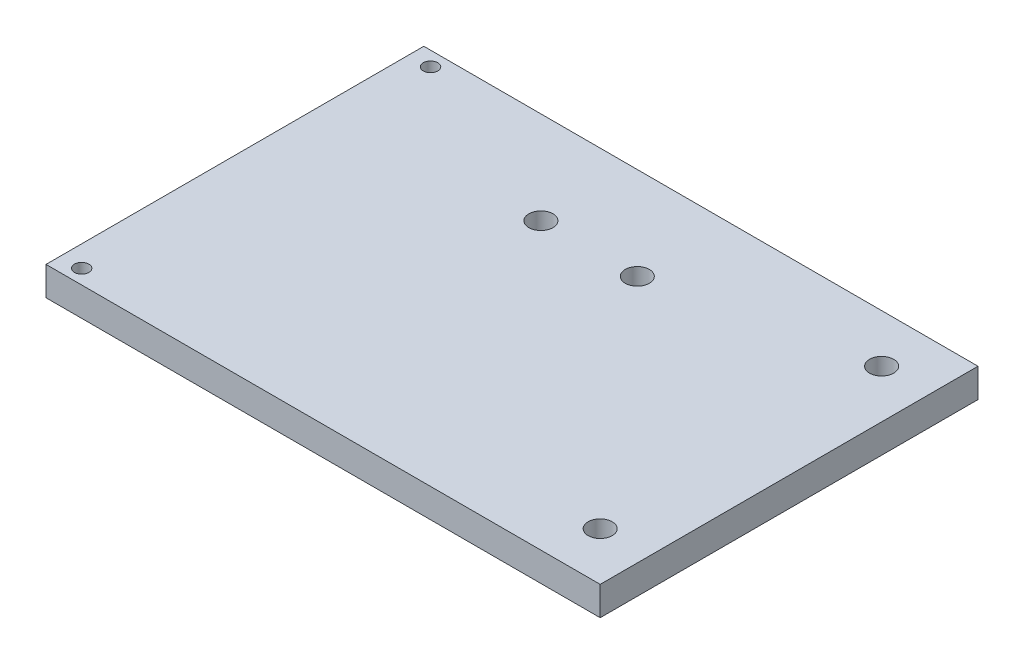
SolidWorks part; units mm, degrees
ref_plane "Front Plane" through (0, 0, 0) normal (0, 0, 1) x (1, 0, 0)
ref_plane "Top Plane" through (0, 0, 0) normal (0, 1, 0) x (1, 0, 0)
ref_plane "Right Plane" through (0, 0, 0) normal (1, 0, 0) x (0, 0, -1)
sketch "Sketch1" plane through (0, 0, 0) normal (0, 1, 0) x (1, 0, 0)
  line L0 (47.5, 29.2) -> (57.5, 29.2) construction
  line L1 (-57.5, -39.2) -> (57.5, -39.2)
  line L2 (-57.5, -39.2) -> (-57.5, 39.2)
  line L3 (-57.5, 39.2) -> (57.5, 39.2)
  line L4 (57.5, -39.2) -> (57.5, 39.2)
  line L5 (-57.5, -39.2) -> (57.5, 39.2) construction
  line L6 (-57.5, 39.2) -> (57.5, -39.2) construction
  line L7 (47.5, -29.2) -> (57.5, -29.2) construction
  circle A0 centre (-53.0995, 36.2) radius 1.5
  circle A1 centre (-53.0995, -36.2) radius 1.5
  circle A2 centre (47.5, 29.2) radius 2.5
  circle A3 centre (47.5, -29.2) radius 2.5
  circle A4 centre (6, 20) radius 2.5
  circle A5 centre (-14, 20) radius 2.5
  point P0 (0, 0)
  point P22 (2.0805, 11.9351)
  dimension "D5" = 5
  dimension "D6" = 5
  dimension "D8" = 3
  dimension "D12" = 5
  dimension "D1" = 115
  dimension "D2" = 78.4
  dimension "D3" = 10
  dimension "D4" = 10
  dimension "D7" = 10
  dimension "D9" = 3
  dimension "D10" = 3
  dimension "D11" = 20
  dimension "D13" = 6
  dimension "D14" = 20
extrude "Boss-Extrude1" add sketch "Sketch1" along normal blind 6
